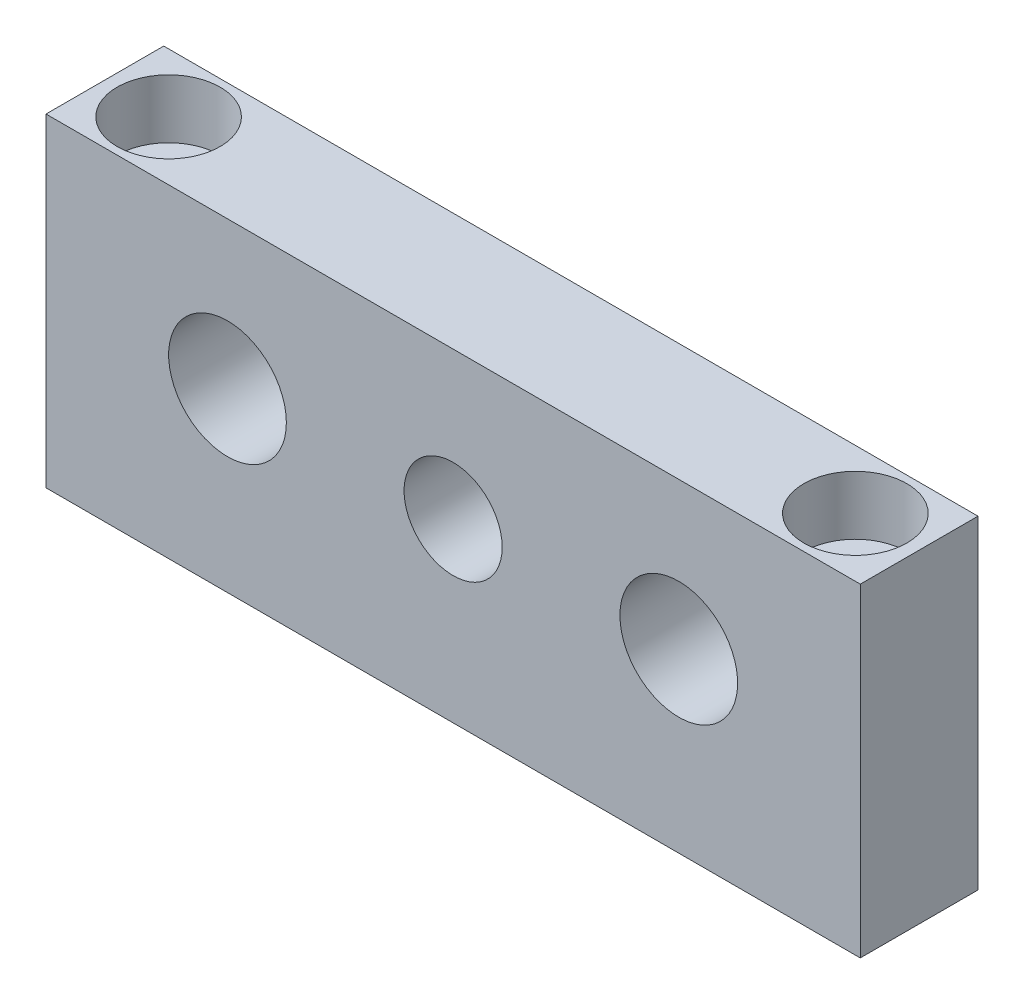
SolidWorks part; units mm, degrees
ref_plane "Front Plane" through (0, 0, 0) normal (0, 0, 1) x (1, 0, 0)
ref_plane "Top Plane" through (0, 0, 0) normal (0, 1, 0) x (1, 0, 0)
ref_plane "Right Plane" through (0, 0, 0) normal (1, 0, 0) x (0, 0, -1)
sketch "Sketch1" plane through (0, 0, 0) normal (0, 0, 1) x (1, 0, 0)
  line L1 (-41.5, -16.5) -> (41.5, -16.5)
  line L2 (-41.5, -16.5) -> (-41.5, 16.5)
  line L3 (-41.5, 16.5) -> (41.5, 16.5)
  line L4 (41.5, -16.5) -> (41.5, 16.5)
  line L5 (-41.5, -16.5) -> (41.5, 16.5) construction
  line L6 (-41.5, 16.5) -> (41.5, -16.5) construction
  point P0 (0, 0)
  dimension "D1" = 83
  dimension "D2" = 33
extrude "Boss-Extrude1" add sketch "Sketch1" along normal blind 12
sketch "Sketch2" plane through (0, 0, 12) normal (0, 0, 1) x (1, 0, 0)
  line L0 (-49.874, 1.5) -> (51.8136, 1.5) construction
  line L1 (41.5, 16.5) -> (-41.5, 16.5) construction
  line L2 (0, 26.2762) -> (0, -24.9832) construction
  circle A0 centre (0, 1.5) radius 5
  circle A1 centre (-23, 1.5) radius 6
  circle A2 centre (23, 1.5) radius 6
  dimension "D2" = 10
  dimension "D3" = 12
  dimension "D1" = 15
  dimension "D4" = 23
extrude "Cut-Extrude1" cut sketch "Sketch2" against normal through all
sketch "Sketch3" plane through (0, 16.5, 0) normal (0, 1, 0) x (1, 0, 0)
  line L0 (-46.6373, -6) -> (46.1838, -6) construction
  line L1 (0, 17.4131) -> (0, -28.2124) construction
  circle A1 centre (-35, -6) radius 3
  circle A2 centre (35, -6) radius 3
  dimension "D1" = 6
  dimension "D2" = 35
extrude "Cut-Extrude2" cut sketch "Sketch3" against normal through all
sketch "Sketch4" plane through (0, 16.5, 0) normal (0, 1, 0) x (1, 0, 0)
  circle A0 centre (-35, -6) radius 5.25
  circle A1 centre (35, -6) radius 5.25
  dimension "D1" = 10.5
extrude "Cut-Extrude3" cut sketch "Sketch4" against normal blind 6
sketch "Sketch5" plane through (0, -16.5, 0) normal (0, -1, 0) x (1, 0, 0)
  line L0 (0, 29.528) -> (0, -12.4692) construction
